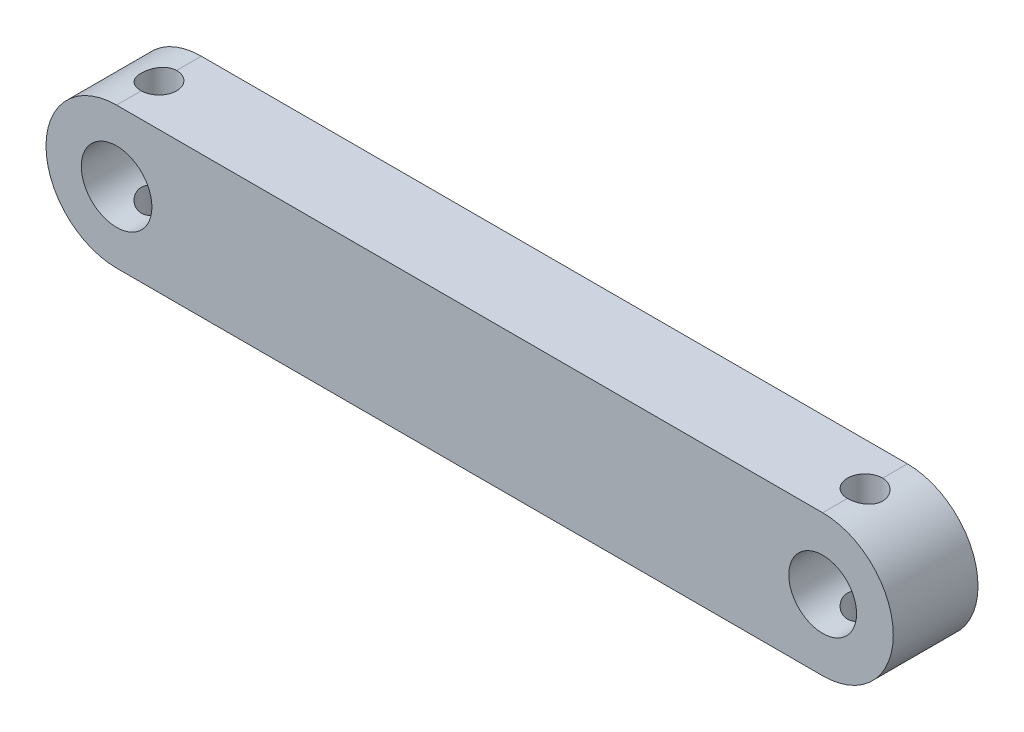
SolidWorks part; units mm, degrees
material "AISI 304"
ref_plane "Front Plane" through (0, 0, 0) normal (0, 0, 1) x (1, 0, 0)
ref_plane "Top Plane" through (0, 0, 0) normal (0, 1, 0) x (1, 0, 0)
ref_plane "Right Plane" through (0, 0, 0) normal (1, 0, 0) x (0, 0, -1)
sketch "Sketch1" plane through (0, 0, 0) normal (0, 0, 1) x (1, 0, 0)
  line L0 (-39.717, 17.4528) -> (10.283, 17.4528) construction
  line L1 (-39.717, 22.4528) -> (10.283, 22.4528)
  line L2 (-39.717, 12.4528) -> (10.283, 12.4528)
  arc A0 (-39.717, 22.4528) -> (-39.717, 12.4528) centre (-39.717, 17.4528) ccw
  arc A1 (10.283, 12.4528) -> (10.283, 22.4528) centre (10.283, 17.4528) ccw
  circle A2 centre (10.283, 17.4528) radius 2.4
  circle A3 centre (-39.717, 17.4528) radius 2.5
  point P2 (-14.717, 17.4528)
  dimension "D1" = 5
  dimension "D2" = 5
  dimension "D3" = 50
extrude "Boss-Extrude1" add sketch "Sketch1" along normal blind 6
sketch "Sketch2" plane through (0, 22.4528, 0) normal (0, 1, 0) x (1, 0, 0)
  line L0 (-39.717, -6) -> (-39.717, 0) construction
  line L1 (10.283, -6) -> (10.283, 0) construction
  circle A0 centre (-39.717, -3) radius 1.25
  circle A1 centre (10.283, -3) radius 1.25
  dimension "D1" = 2.5
  dimension "D2" = 2.5
extrude "Cut-Extrude1" cut sketch "Sketch2" against normal through all both and the other way through all
